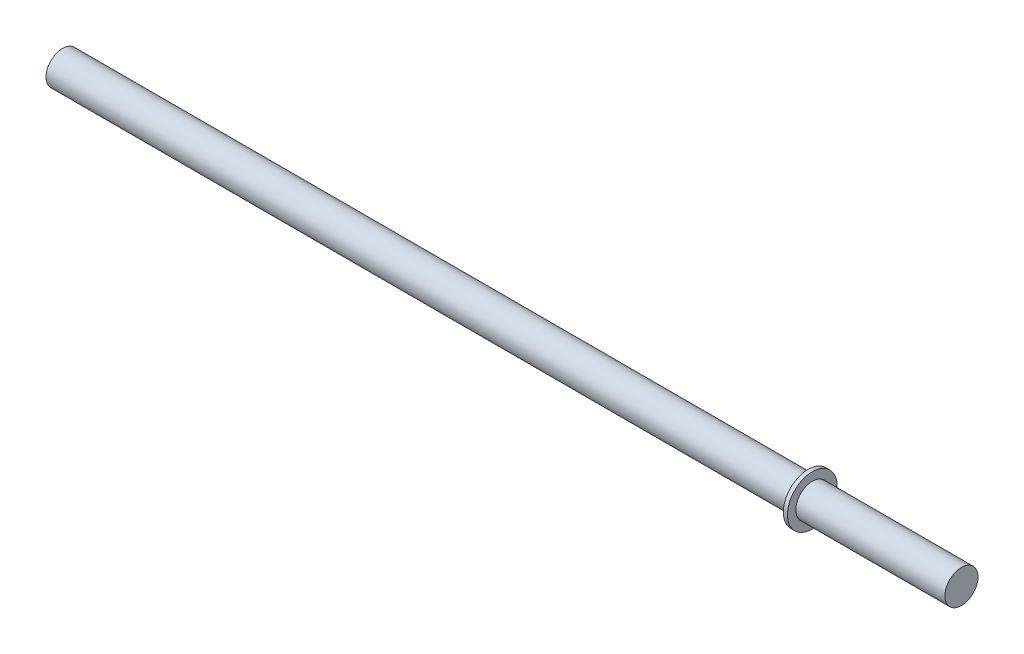
SolidWorks part; units mm, degrees
material "Stal stopowa"
ref_plane "Płaszczyzna XY" through (0, 0, 0) normal (0, 0, 1) x (1, 0, 0)
ref_plane "Płaszczyzna XZ" through (0, 0, 0) normal (0, 1, 0) x (1, 0, 0)
ref_plane "Płaszczyzna YZ" through (0, 0, 0) normal (1, 0, 0) x (0, 0, -1)
sketch "Szkic1" plane through (0, 0, 0) normal (0, 0, 1) x (1, 0, 0)
  line L0 (0, 0) -> (108.5, 0) construction
  line L1 (0, 0) -> (0, 2)
  line L2 (0, 2) -> (90, 2)
  line L3 (90, 2) -> (90, 3)
  line L4 (90, 3) -> (90.5, 3)
  line L5 (90.5, 3) -> (90.5, 2)
  line L6 (90.5, 2) -> (108.5, 2)
  line L7 (108.5, 2) -> (108.5, 0)
  line L8 (0, 0) -> (108.5, 0)
  dimension "D1" = 0.5
  dimension "D2" = 6
  dimension "D3" = 18
  dimension "D4" = 90
  dimension "D5" = 4
revolve "Obrót1" add sketch "Szkic1" angle 360 about L0
